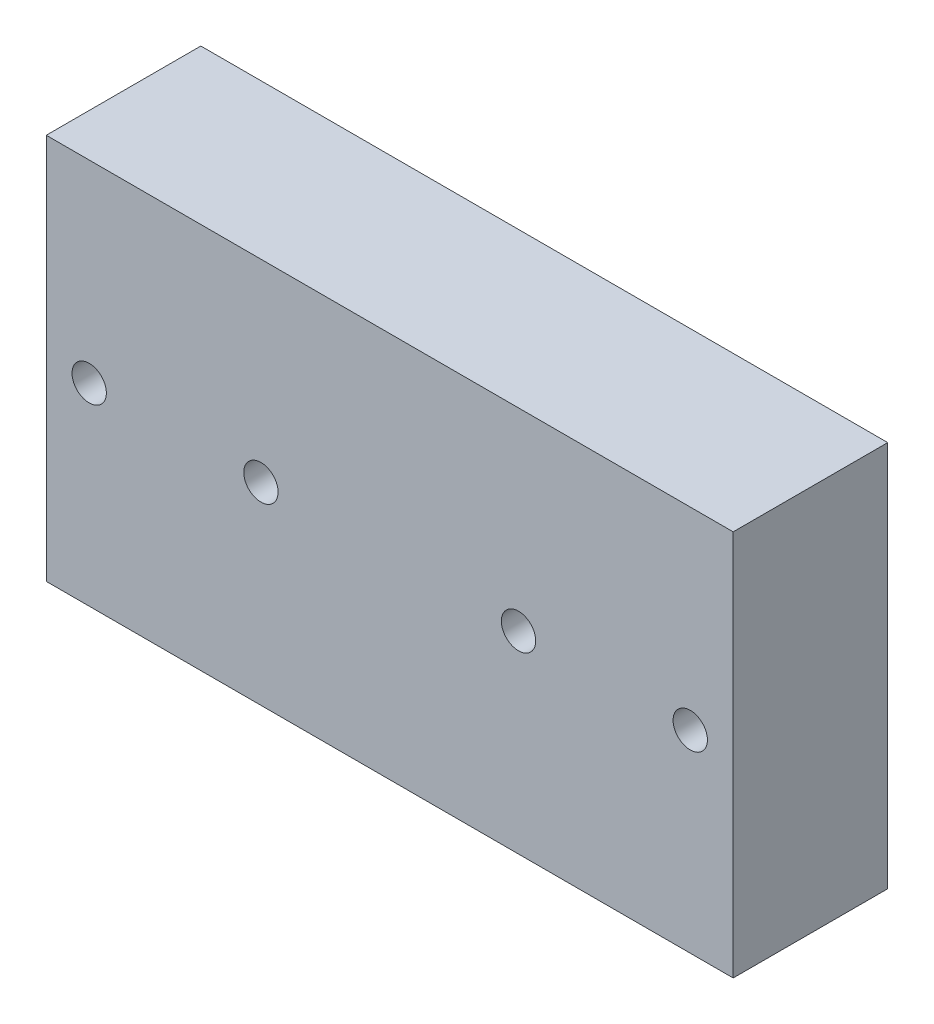
SolidWorks part; units mm, degrees
ref_plane "Front Plane" through (0, 0, 0) normal (0, 0, 1) x (1, 0, 0)
ref_plane "Top Plane" through (0, 0, 0) normal (0, 1, 0) x (1, 0, 0)
ref_plane "Right Plane" through (0, 0, 0) normal (1, 0, 0) x (0, 0, -1)
sketch "Sketch1" plane through (0, 0, 0) normal (0, 0, 1) x (1, 0, 0)
  line L0 (-543.3265, 0) -> (26623.0008, 0) construction
  line L1 (0, -543.3265) -> (0, 26623.0008) construction
  line L2 (25, -543.3265) -> (25, 26623.0008) construction
  line L3 (-40, -22.5) -> (40, -22.5)
  line L4 (-40, -22.5) -> (-40, 22.5)
  line L5 (-40, 22.5) -> (40, 22.5)
  line L6 (40, -22.5) -> (40, 22.5)
  line L7 (-25, -543.3265) -> (-25, 26623.0008) construction
  circle A0 centre (35, 0) radius 2
  circle A1 centre (15, 0) radius 2
  circle A2 centre (-15, 0) radius 2
  circle A3 centre (-35, 0) radius 2
  point P9 (0, 22.5)
  point P10 (-40, 0)
  dimension "D5" = 4
  dimension "D1" = 45
  dimension "D2" = 80
  dimension "D6" = 10
  dimension "D3" = 25
  dimension "D4" = 25
extrude "Boss-Extrude1" add sketch "Sketch1" along normal blind 18
